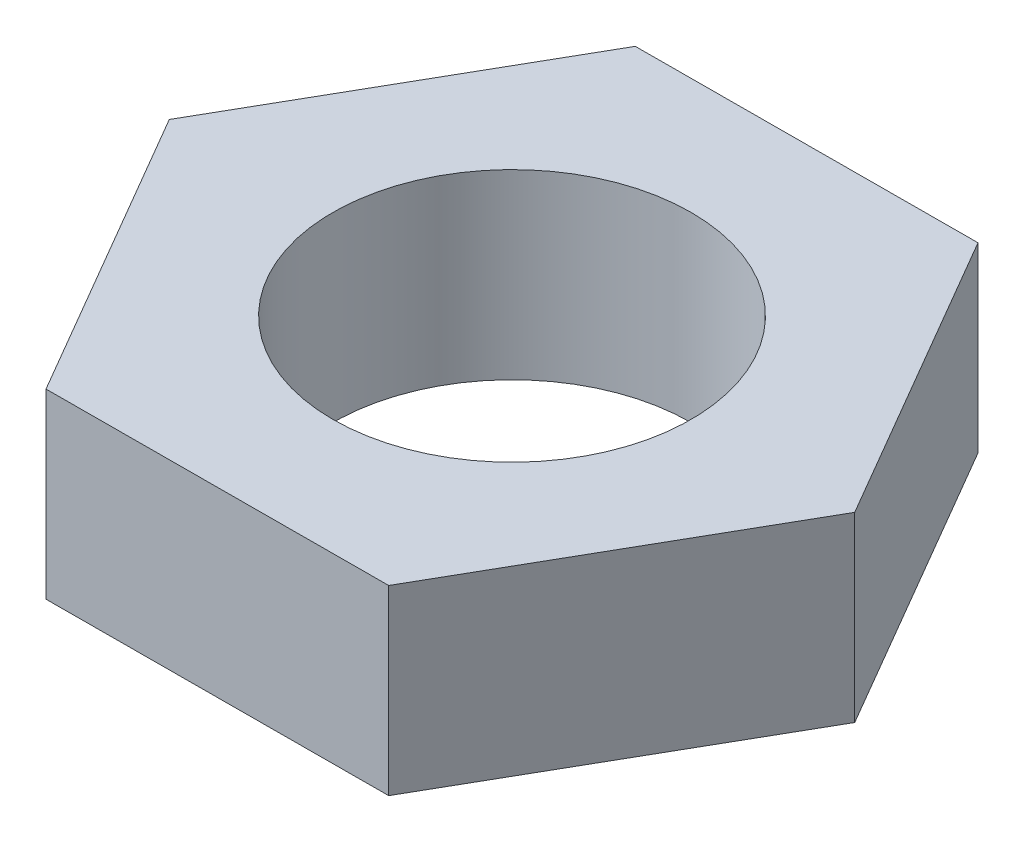
SolidWorks part; units mm, degrees
ref_plane "Front Plane" through (0, 0, 0) normal (0, 0, 1) x (1, 0, 0)
ref_plane "Top Plane" through (0, 0, 0) normal (0, 1, 0) x (1, 0, 0)
ref_plane "Right Plane" through (0, 0, 0) normal (1, 0, 0) x (0, 0, -1)
sketch "Sketch1" plane through (0, 0, 0) normal (0, 1, 0) x (1, 0, 0)
  line L1 (7.6938, 13.4395) -> (-7.792, 13.3828)
  line L2 (-7.792, 13.3828) -> (-15.4858, -0.0567)
  line L3 (-15.4858, -0.0567) -> (-7.6938, -13.4395)
  line L4 (-7.6938, -13.4395) -> (7.792, -13.3828)
  line L5 (7.792, -13.3828) -> (15.4858, 0.0567)
  line L6 (15.4858, 0.0567) -> (7.6938, 13.4395)
  circle A0 centre (0, 0) radius 13.4112 construction
  dimension "D1" = 26.8224
extrude "Boss-Extrude1" add sketch "Sketch1" along normal blind 8.255 contours L1 L2 L3 L4 L5 L6
sketch "Sketch2" plane through (0, 8.255, 0) normal (0, 1, 0) x (1, 0, 0)
  circle A0 centre (0, 0) radius 8.128
extrude "Cut-Extrude1" cut sketch "Sketch2" against normal through all
